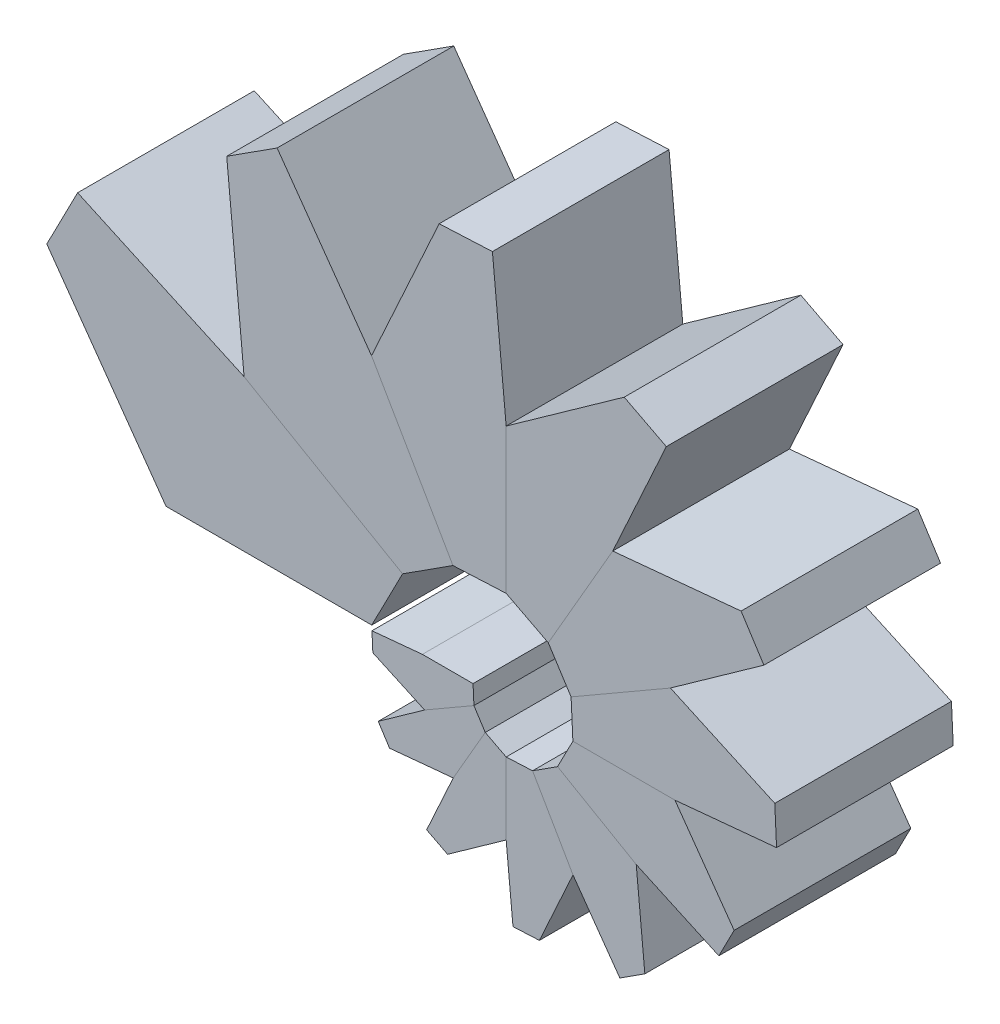
SolidWorks part; units mm, degrees
ref_plane "Plan de face" through (0, 0, 0) normal (0, 0, 1) x (1, 0, 0)
ref_plane "Plan de dessus" through (0, 0, 0) normal (0, 1, 0) x (1, 0, 0)
ref_plane "Plan de droite" through (0, 0, 0) normal (1, 0, 0) x (0, 0, -1)
sketch "Esquisse1" plane through (0, 0, 0) normal (0, 0, 1) x (1, 0, 0)
  line L1 (-32.4091, 0) -> (0, 0) construction
  spline S0 degree 4 number of poles 92 (-1.8486, -2.3147) -> (-32.7346, -11.5727) construction
  spline S1 degree 4 number of poles 65 (0, 0) -> (-32.4091, 0)
sketch "Esquisse11" plane through (0, 0, 0) normal (0, 0, 1) x (1, 0, 0)
  line L0 (2.1349, 0) -> (-2.1349, 0) construction
  line L1 (2.1349, 0) -> (19.4696, 0) construction
  spline S0 degree 4 number of poles 100 (-3.2046, -1.0028) -> (19.6183, 9.858) construction
  spline S1 degree 4 number of poles 72 (-2.1349, 0) -> (19.4696, 0)
  point P5 (0, 0)
sketch "Esquisse19" plane through (0, 0, 0) normal (0, 0, 1) x (1, 0, 0)
  line L2 (-3.5303, 0) -> (-32.4091, 0) construction
  line L3 (-3.5303, 0) -> (-28.5401, 14.4394) construction
  line L4 (-3.5303, 0) -> (-17.9697, 25.0098) construction
  line L5 (-3.5303, 0) -> (-3.5303, 28.8788) construction
  line L6 (-3.5303, 0) -> (10.9091, 25.0098) construction
  line L7 (-3.5303, 0) -> (21.4795, 14.4394) construction
  line L8 (-3.5303, 0) -> (25.3485, 0) construction
  line L9 (-3.5303, 0) -> (21.4795, -14.4394) construction
  line L10 (-3.5303, 0) -> (10.9091, -25.0098) construction
  line L11 (-3.5303, 0) -> (-3.5303, -28.8788) construction
  line L12 (-3.5303, 0) -> (-17.9697, -25.0098) construction
  line L13 (-3.5303, 0) -> (-28.5401, -14.4394) construction
  spline S0 degree 4 number of poles 72 (-2.1349, 0) -> (19.4696, 0) construction
  point P0 (-3.7061, 0)
  point P11 (-14.9452, 0)
  point P24 (-3.5303, 0)
  dimension "D2" = 3.5303
  dimension "D1" = 12
sketch "Esquisse20" plane through (0, 0, 0) normal (0, 0, 1) x (1, 0, 0)
  line L0 (-10.6435, 0) -> (-6.342, 0)
  line L1 (-32.4091, 0) -> (0, 0) construction
  line L2 (-6.342, 0) -> (-6.2669, -1.58)
  line L3 (-3.5303, 0) -> (-28.5401, -14.4394) construction
  line L4 (-6.2669, -1.58) -> (-10.4535, -3.9971)
  line L5 (-10.4535, -3.9971) -> (-10.6435, 0)
  spline S0 degree 4 number of poles 65 (0, 0) -> (-32.4091, 0) construction
  spline S1 degree 4 number of poles 72 (-2.1349, 0) -> (19.4696, 0) construction
  point P13 (0, 0)
extrude "Boss.-Extru.1" add sketch "Esquisse20" along normal mid plane 15 contours L0 L2 L4 L5
sketch "Esquisse21" plane through (0, 0, 0) normal (0, 0, 1) x (1, 0, 0)
  line L0 (-5.3059, -3.0755) -> (-8.0225, -7.7806)
  line L1 (-3.5303, 0) -> (-17.9697, -25.0098) construction
  line L2 (-8.0225, -7.7806) -> (-3.5303, -10.0971)
  line L3 (-3.5303, 0) -> (-3.5303, -28.8788) construction
  line L4 (-3.5303, -10.0971) -> (-3.5303, -3.9911)
  line L5 (-3.5303, -3.9911) -> (-5.3059, -3.0755)
  spline S0 degree 4 number of poles 72 (-2.1349, 0) -> (19.4696, 0) construction
  spline S1 degree 4 number of poles 65 (0, 0) -> (-32.4091, 0) construction
extrude "Boss.-Extru.3" add sketch "Esquisse21" along normal mid plane 15 separate body
sketch "Esquisse22" plane through (0, 0, 0) normal (0, 0, 1) x (1, 0, 0)
  line L0 (-6.2669, -1.58) -> (-5.3059, -3.0755)
  line L1 (-5.3059, -3.0755) -> (-8.0225, -7.7806)
  line L2 (-8.0225, -7.7806) -> (-10.4535, -3.9971)
  line L3 (-10.4535, -3.9971) -> (-6.2669, -1.58)
extrude "Boss.-Extru.4" add sketch "Esquisse22" along normal mid plane 15 separate body
sketch "Esquisse23" plane through (0, 0, 0) normal (0, 0, 1) x (1, 0, 0)
  line L0 (-3.5303, -3.9911) -> (-1.2877, -3.8843)
  line L1 (-3.5303, 0) -> (10.9091, -25.0098) construction
  line L2 (-1.2877, -3.8843) -> (2.1435, -9.8273)
  line L3 (2.1435, -9.8273) -> (-3.5303, -10.0971)
  line L4 (-3.5303, 0) -> (-3.5303, -28.8788) construction
  line L5 (-3.5303, -10.0971) -> (-3.5303, -3.9911)
  spline S0 degree 4 number of poles 72 (-2.1349, 0) -> (19.4696, 0) construction
  spline S1 degree 4 number of poles 65 (0, 0) -> (-32.4091, 0) construction
extrude "Boss.-Extru.5" add sketch "Esquisse23" along normal mid plane 15 separate body
sketch "Esquisse24" plane through (0, 0, 0) normal (0, 0, 1) x (1, 0, 0)
  line L0 (-1.2877, -3.8843) -> (0.8353, -2.5205)
  line L1 (-3.5303, 0) -> (21.4795, -14.4394) construction
  line L2 (0.8353, -2.5205) -> (7.5141, -6.3765)
  line L3 (7.5141, -6.3765) -> (2.1435, -9.8273)
  line L4 (2.1435, -9.8273) -> (-1.2877, -3.8843)
  spline S0 degree 4 number of poles 72 (-2.1349, 0) -> (19.4696, 0) construction
  spline S1 degree 4 number of poles 65 (0, 0) -> (-32.4091, 0) construction
extrude "Boss.-Extru.6" add sketch "Esquisse24" along normal mid plane 15 separate body
sketch "Esquisse25" plane through (0, 0, 0) normal (0, 0, 1) x (1, 0, 0)
  line L0 (7.5141, -6.3765) -> (10.8021, 0)
  line L1 (2.1349, 0) -> (19.4696, 0) construction
  line L2 (10.8021, 0) -> (2.1349, 0)
  line L3 (2.1349, 0) -> (0.8353, -2.5205)
  line L4 (0.8353, -2.5205) -> (7.5141, -6.3765)
  spline S0 degree 4 number of poles 65 (0, 0) -> (-32.4091, 0) construction
extrude "Boss.-Extru.7" add sketch "Esquisse25" along normal mid plane 15 separate body
sketch "Esquisse26" plane through (0, 0, 0) normal (0, 0, 1) x (1, 0, 0)
  line L0 (10.8021, 0) -> (2.1349, 0)
  line L2 (2.1349, 0) -> (1.9835, 3.1834)
  line L3 (-3.5303, 0) -> (21.4795, 14.4394) construction
  line L4 (1.9835, 3.1834) -> (10.4193, 8.0538)
  line L5 (10.4193, 8.0538) -> (10.8021, 0)
  spline S0 degree 4 number of poles 72 (-2.1349, 0) -> (19.4696, 0) construction
  spline S1 degree 4 number of poles 65 (0, 0) -> (-32.4091, 0) construction
extrude "Boss.-Extru.8" add sketch "Esquisse26" along normal mid plane 15 separate body
sketch "Esquisse27" plane through (0, 0, 0) normal (0, 0, 1) x (1, 0, 0)
  line L0 (1.9835, 3.1834) -> (10.4193, 8.0538)
  line L1 (10.4193, 8.0538) -> (5.521, 15.6773)
  line L2 (-3.5303, 0) -> (10.9091, 25.0098) construction
  line L3 (5.521, 15.6773) -> (0.0474, 6.1967)
  line L4 (0.0474, 6.1967) -> (1.9835, 3.1834)
  spline S0 degree 4 number of poles 65 (0, 0) -> (-32.4091, 0) construction
  spline S1 degree 4 number of poles 72 (-2.1349, 0) -> (19.4696, 0) construction
extrude "Boss.-Extru.9" add sketch "Esquisse27" along normal mid plane 15 separate body
sketch "Esquisse28" plane through (0, 0, 0) normal (0, 0, 1) x (1, 0, 0)
  line L0 (0.0474, 6.1967) -> (-3.5303, 8.0417)
  line L1 (-3.5303, 0) -> (-3.5303, 28.8788) construction
  line L2 (-3.5303, 8.0417) -> (-3.5303, 20.3447)
  line L3 (-3.5303, 20.3447) -> (5.521, 15.6773)
  line L4 (5.521, 15.6773) -> (0.0474, 6.1967)
  spline S0 degree 4 number of poles 72 (-2.1349, 0) -> (19.4696, 0) construction
  spline S1 degree 4 number of poles 65 (0, 0) -> (-32.4091, 0) construction
extrude "Boss.-Extru.10" add sketch "Esquisse28" along normal mid plane 15 separate body
sketch "Esquisse29" plane through (0, 0, 0) normal (0, 0, 1) x (1, 0, 0)
  line L0 (-3.5303, 8.0417) -> (-8.0491, 7.8268)
  line L1 (-3.5303, 0) -> (-17.9697, 25.0098) construction
  line L2 (-8.0491, 7.8268) -> (-14.9625, 19.8012)
  line L3 (-14.9625, 19.8012) -> (-3.5303, 20.3447)
  line L4 (-3.5303, 20.3447) -> (-3.5303, 8.0417)
  spline S0 degree 4 number of poles 72 (-2.1349, 0) -> (19.4696, 0) construction
  spline S1 degree 4 number of poles 65 (0, 0) -> (-32.4091, 0) construction
extrude "Boss.-Extru.11" add sketch "Esquisse29" along normal mid plane 15 separate body
sketch "Esquisse30" plane through (0, 0, 0) normal (0, 0, 1) x (1, 0, 0)
  line L0 (-8.0491, 7.8268) -> (-14.9625, 19.8012)
  line L1 (-14.9625, 19.8012) -> (-25.7839, 12.8481)
  line L2 (-3.5303, 0) -> (-28.5401, 14.4394) construction
  line L3 (-25.7839, 12.8481) -> (-12.3262, 5.0783)
  line L4 (-12.3262, 5.0783) -> (-8.0491, 7.8268)
  spline S0 degree 4 number of poles 65 (0, 0) -> (-32.4091, 0) construction
  spline S1 degree 4 number of poles 72 (-2.1349, 0) -> (19.4696, 0) construction
extrude "Boss.-Extru.12" add sketch "Esquisse30" along normal mid plane 15 separate body
sketch "Esquisse31" plane through (0, 0, 0) normal (0, 0, 1) x (1, 0, 0)
  line L0 (-25.7839, 12.8481) -> (-12.3262, 5.0783)
  line L1 (-12.3262, 5.0783) -> (-14.9452, 0)
  line L2 (-14.9452, 0) -> (-32.4091, 0)
  line L3 (-32.4091, 0) -> (-25.7839, 12.8481)
extrude "Boss.-Extru.13" add sketch "Esquisse31" along normal mid plane 15 separate body
mirror "Symétrie1" about plane through (-10.4535, -3.9971, 7.5) normal (-0.9989, -0.0475, 0) of bodies 108
mirror "Symétrie2" about plane through (-8.0225, -7.7806, 7.5) normal (0.8413, 0.5406, 0) of bodies 111
mirror "Symétrie3" about plane through (-8.0225, -7.7806, 7.5) normal (0.4583, 0.8888, 0) of bodies 110
mirror "Symétrie4" about plane through (2.1435, -9.8273, 7.5) normal (-0.0475, 0.9989, 0) of bodies 112
mirror "Symétrie5" about plane through (7.5141, -6.3765, 7.5) normal (-0.5406, 0.8413, 0) of bodies 113
mirror "Symétrie6" about plane through (7.5141, -6.3765, 7.5) normal (-0.8888, 0.4583, 0) of bodies 114
mirror "Symétrie7" about plane through (10.4193, 8.0538, 7.5) normal (-0.9989, -0.0475, 0) of bodies 115
mirror "Symétrie8" about plane through (10.4193, 8.0538, 7.5) normal (-0.8413, -0.5406, 0) of bodies 116
mirror "Symétrie9" about plane through (-3.5303, 20.3447, 7.5) normal (-0.4583, -0.8888, 0) of bodies 117
mirror "Symétrie10" about plane through (-14.9625, 19.8012, 7.5) normal (0.0475, -0.9989, 0) of bodies 118
mirror "Symétrie11" about plane through (-14.9625, 19.8012, 7.5) normal (0.5406, -0.8413, 0) of bodies 119
mirror "Symétrie12" about plane through (-32.4091, 0, 7.5) normal (0.8888, -0.4583, 0) of bodies 120
other "Enregistrer les corps1"
